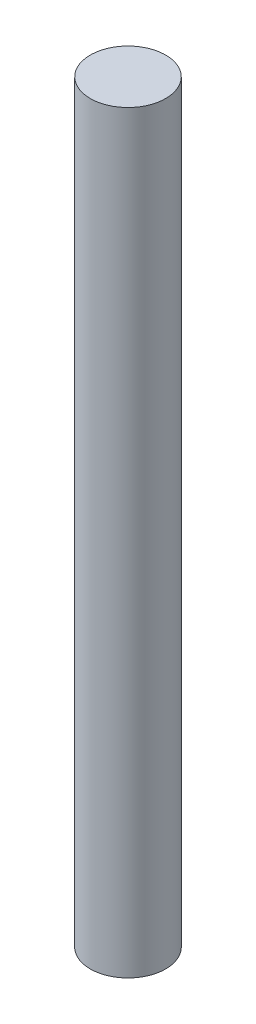
SolidWorks part; units mm, degrees
ref_plane "Alzado" through (0, 0, 0) normal (0, 0, 1) x (1, 0, 0)
ref_plane "Planta" through (0, 0, 0) normal (0, 1, 0) x (1, 0, 0)
ref_plane "Vista lateral" through (0, 0, 0) normal (1, 0, 0) x (0, 0, -1)
sketch "Croquis1" plane through (0, 0, 0) normal (0, 1, 0) x (1, 0, 0)
  circle A0 centre (0, 0) radius 1.5
  dimension "D1" = 3
extrude "Saliente-Extruir1" add sketch "Croquis1" along normal blind 30
